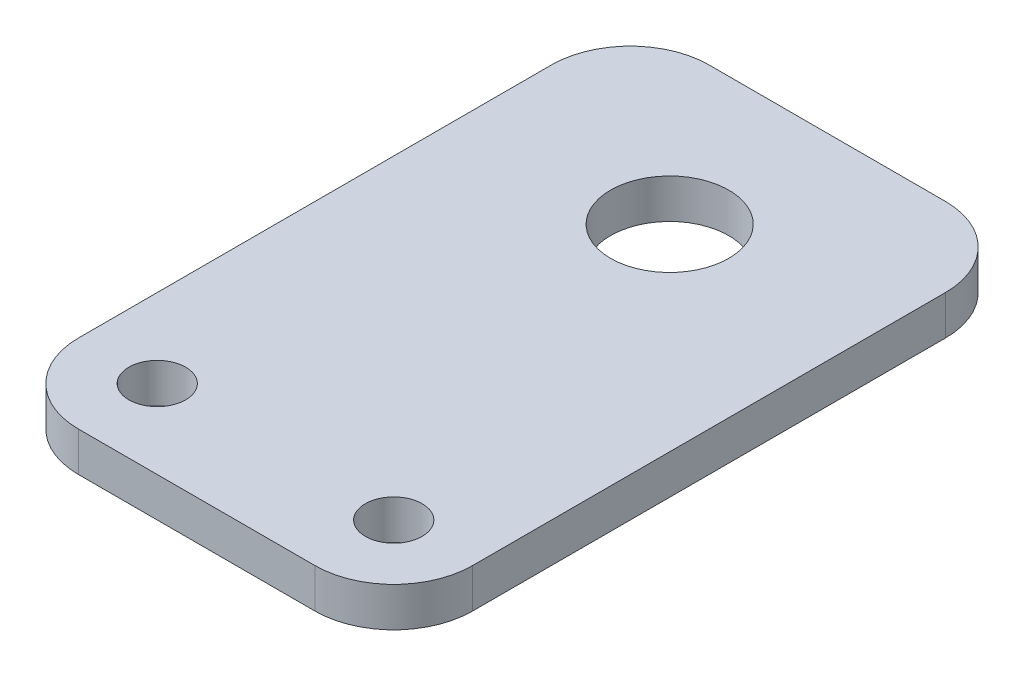
SolidWorks part; units mm, degrees
ref_plane "Front Plane" through (0, 0, 0) normal (0, 0, 1) x (1, 0, 0)
ref_plane "Top Plane" through (0, 0, 0) normal (0, 1, 0) x (1, 0, 0)
ref_plane "Right Plane" through (0, 0, 0) normal (1, 0, 0) x (0, 0, -1)
sketch "Sketch1" plane through (0, 0, 0) normal (0, 1, 0) x (1, 0, 0)
  line L0 (6.35, 6.35) -> (25.4, 6.35) construction
  line L1 (0, 0) -> (31.75, 0)
  line L2 (0, 0) -> (0, 50.8)
  line L3 (0, 50.8) -> (31.75, 50.8)
  line L4 (31.75, 0) -> (31.75, 50.8)
  circle A0 centre (15.875, 38.1) radius 4.7625
  circle A1 centre (6.35, 6.35) radius 2.286
  circle A2 centre (25.4, 6.35) radius 2.286
  point P11 (15.875, 0)
  point P12 (15.875, 6.35)
  point P13 (0, 0)
  dimension "D5" = 4.572
  dimension "D6" = 9.525
  dimension "D1" = 31.75
  dimension "D2" = 50.8
  dimension "D3" = 19.05
  dimension "D4" = 6.35
  dimension "D7" = 12.7
extrude "Boss-Extrude1" add sketch "Sketch1" along normal blind 3.175
fillet "Fillet1" radius 6.35 4 edges at (31.75, 1.5875, 0) (31.75, 1.5875, -50.8) (0, 1.5875, -50.8) (0, 1.5875, 0)
